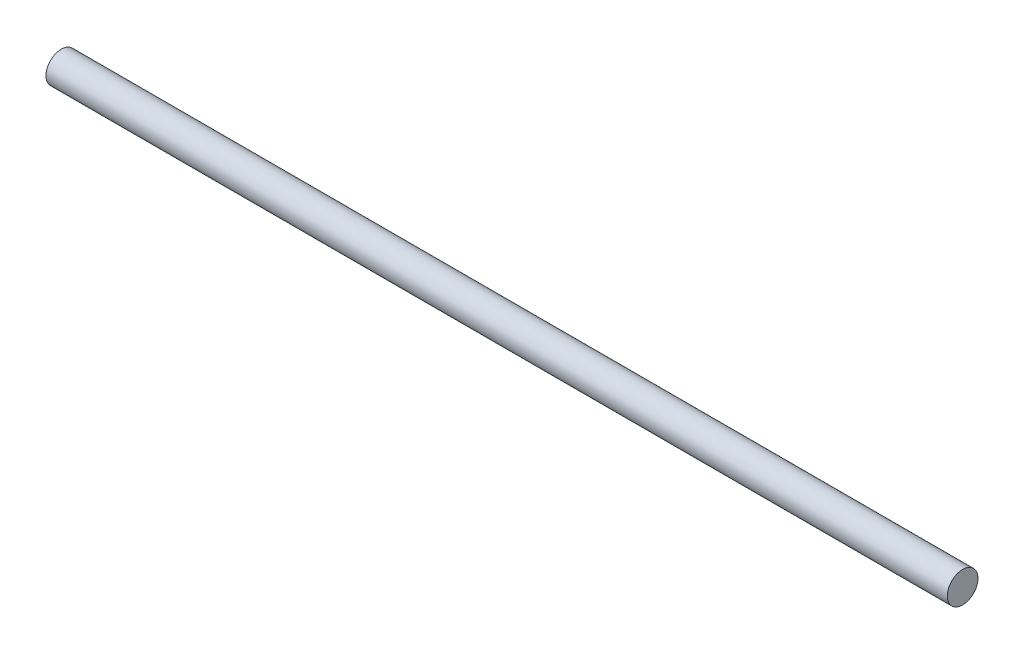
SolidWorks part; units mm, degrees
ref_plane "Front Plane" through (0, 0, 0) normal (0, 0, 1) x (1, 0, 0)
ref_plane "Top Plane" through (0, 0, 0) normal (0, 1, 0) x (1, 0, 0)
ref_plane "Right Plane" through (0, 0, 0) normal (1, 0, 0) x (0, 0, -1)
sketch "Sketch1" plane through (0, 0, 0) normal (1, 0, 0) x (0, 0, -1)
  circle A0 centre (0, 0) radius 6
  dimension "D1" = 12
extrude "Boss-Extrude1" add sketch "Sketch1" along normal mid plane 351.65
